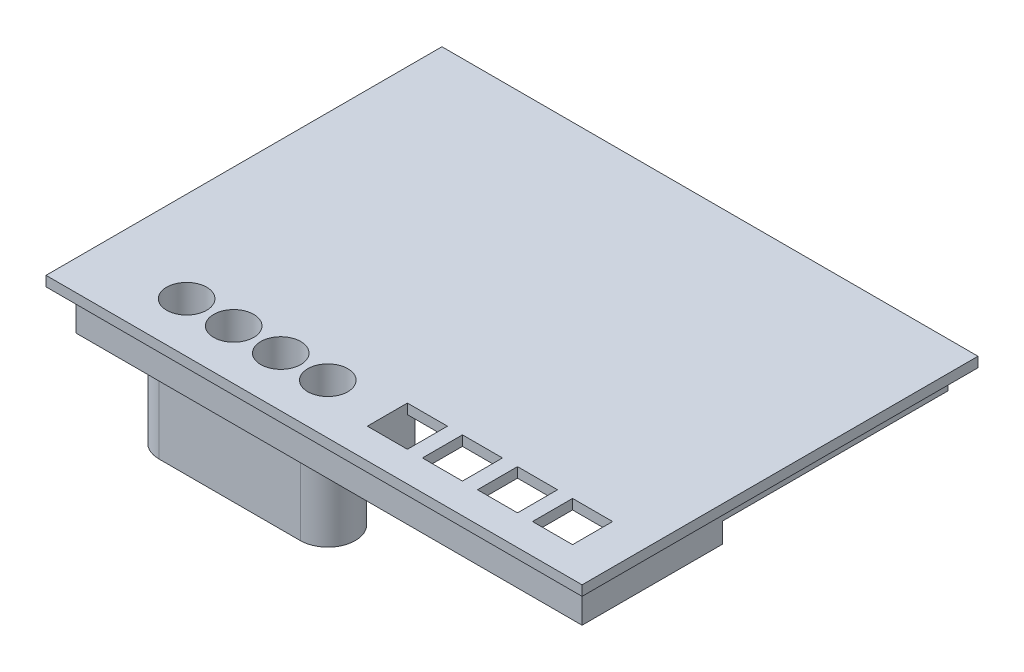
SolidWorks part; units mm, degrees
ref_plane "Front Plane" through (0, 0, 0) normal (0, 0, 1) x (1, 0, 0)
ref_plane "Top Plane" through (0, 0, 0) normal (0, 1, 0) x (1, 0, 0)
ref_plane "Right Plane" through (0, 0, 0) normal (1, 0, 0) x (0, 0, -1)
sketch "Sketch1" plane through (0, 0, 0) normal (0, 1, 0) x (1, 0, 0)
  line L1 (-39.05, -27.95) -> (39.05, -27.95)
  line L2 (-39.05, -27.95) -> (-39.05, 27.95)
  line L3 (-39.05, 27.95) -> (39.05, 27.95)
  line L4 (39.05, -27.95) -> (39.05, 27.95)
  line L5 (-39.05, -27.95) -> (39.05, 27.95) construction
  line L6 (-39.05, 27.95) -> (39.05, -27.95) construction
  point P0 (0, 0)
extrude "Boss-Extrude1" add sketch "Sketch1" along normal blind 3
sketch "Sketch2" plane through (0, 3, 0) normal (0, 1, 0) x (1, 0, 0)
  circle A0 centre (-35.9, 20.9) radius 1.25
  circle A1 centre (-35.9, -24.8) radius 1.25
  circle A2 centre (35.9, -24.8) radius 1.25
  circle A3 centre (35.9, 24.8) radius 1.25
extrude "Cut-Extrude1" cut sketch "Sketch2" against normal blind 68
sketch "Sketch3" plane through (0, 3, 0) normal (0, 1, 0) x (1, 0, 0)
  line L0 (-39.05, -27.95) -> (39.05, -27.95) construction
  line L5 (-31.15, -27.95) -> (8.45, -27.95)
  line L6 (-31.15, -27.95) -> (-31.15, -12.75)
  line L7 (-31.15, -12.75) -> (8.45, -12.75)
  line L8 (8.45, -27.95) -> (8.45, -12.75)
  line L13 (27.35, -17.65) -> (15.85, -17.65)
  line L14 (27.35, -17.65) -> (27.35, -27.95)
  line L15 (27.35, -27.95) -> (15.85, -27.95)
  line L16 (15.85, -17.65) -> (15.85, -27.95)
  line L18 (-39.05, 27.95) -> (39.05, 27.95)
  line L19 (-39.05, 27.95) -> (-39.05, -27.95)
  line L20 (-39.05, -27.95) -> (39.05, -27.95)
  line L21 (39.05, 27.95) -> (39.05, -27.95)
  line L22 (-31.15, -27.95) -> (-25.45, -27.95)
  line L23 (-31.15, -27.95) -> (-31.15, -20.45)
  line L24 (-31.15, -20.45) -> (-25.45, -20.45)
  line L25 (-25.45, -27.95) -> (-25.45, -20.45)
  line L26 (8.45, -27.95) -> (2.75, -27.95)
  line L27 (8.45, -27.95) -> (8.45, -20.45)
  line L28 (8.45, -20.45) -> (2.75, -20.45)
  line L29 (2.75, -27.95) -> (2.75, -20.45)
  line L30 (2.75, -27.95) -> (-6.65, -27.95)
  line L31 (2.75, -27.95) -> (2.75, -20.45)
  line L32 (2.75, -20.45) -> (-6.65, -20.45)
  line L33 (-6.65, -27.95) -> (-6.65, -20.45)
  line L34 (-25.45, -27.95) -> (-16.05, -27.95)
  line L35 (-25.45, -27.95) -> (-25.45, -20.45)
  line L36 (-25.45, -20.45) -> (-16.05, -20.45)
  line L37 (-16.05, -27.95) -> (-16.05, -20.45)
  circle A0 centre (35.9, 24.8) radius 1.25
  circle A1 centre (35.9, -24.8) radius 1.25
  circle A2 centre (-35.9, -24.8) radius 1.25
  circle A3 centre (-35.9, 20.9) radius 1.25
  circle A4 centre (2.75, -20.45) radius 4
  circle A5 centre (-6.65, -20.45) radius 4
  circle A6 centre (-16.05, -20.45) radius 4
  circle A7 centre (-25.45, -20.45) radius 4
sketch "Sketch4" plane through (0, 0, 0) normal (0, -1, 0) x (-1, 0, 0)
  line L0 (0, -27.95) -> (0, -29.95) construction
  line L1 (39.05, 27.95) -> (-39.05, 27.95)
  line L2 (39.05, 27.95) -> (39.05, -27.95)
  line L3 (39.05, -27.95) -> (-39.05, -27.95)
  line L4 (-39.05, 27.95) -> (-39.05, -27.95)
  line L5 (39.05, 27.95) -> (-39.05, -27.95) construction
  line L6 (39.05, -27.95) -> (-39.05, 27.95) construction
  line L7 (41.05, 29.95) -> (-41.05, 29.95)
  line L8 (41.05, 29.95) -> (41.05, -29.95)
  line L9 (41.05, -29.95) -> (-41.05, -29.95)
  line L10 (-41.05, 29.95) -> (-41.05, -29.95)
  line L11 (41.05, 29.95) -> (-41.05, -29.95) construction
  line L12 (41.05, -29.95) -> (-41.05, 29.95) construction
  line L13 (-39.05, 0) -> (-41.05, 0) construction
  point P0 (0, 0)
  point P7 (0, 0)
extrude "Boss-Extrude3" add sketch "Sketch4" against normal blind 3
sketch "Sketch6" plane through (0, 3, 0) normal (0, 1, 0) x (1, 0, 0)
  circle A0 centre (-35.9, -24.8) radius 1.25
  circle A1 centre (35.9, -24.8) radius 1.25
  circle A2 centre (35.9, 24.8) radius 1.25
  circle A3 centre (-35.9, 20.9) radius 1.25
  circle A4 centre (-35.9, 20.9) radius 3
  circle A5 centre (35.9, 24.8) radius 3
  circle A6 centre (35.9, -24.8) radius 3
  circle A7 centre (-35.9, -24.8) radius 3
extrude "Boss-Extrude4" add sketch "Sketch6" along normal blind 3.5
sketch "Sketch7" plane through (0, 0, 0) normal (0, -1, 0) x (-1, 0, 0)
  line L1 (-41.05, 29.95) -> (41.05, 29.95)
  line L2 (-41.05, 29.95) -> (-41.05, 46.15)
  line L3 (-41.05, 46.15) -> (41.05, 46.15)
  line L4 (41.05, 29.95) -> (41.05, 46.15)
extrude "Boss-Extrude5" add sketch "Sketch7" against normal blind 3
sketch "Sketch8" plane through (0, 0, -46.15) normal (0, 0, -1) x (-1, 0, 0)
  line L1 (-41.05, 0) -> (41.05, 0)
  line L2 (-41.05, 0) -> (-41.05, 50.5)
  line L3 (-41.05, 50.5) -> (41.05, 50.5)
  line L4 (41.05, 0) -> (41.05, 50.5)
extrude "Boss-Extrude6" add sketch "Sketch8" along normal blind 3
sketch "Sketch10" plane through (41.05, 0, 0) normal (1, 0, 0) x (0, 0, -1)
  line L1 (46.15, 50.5) -> (49.15, 50.5)
  line L2 (46.15, 50.5) -> (46.15, 0)
  line L3 (46.15, 0) -> (49.15, 0)
  line L4 (49.15, 50.5) -> (49.15, 0)
  line L5 (-29.95, 0) -> (46.15, 0)
  line L6 (-29.95, 0) -> (-29.95, 3)
  line L7 (-29.95, 3) -> (46.15, 3)
  line L8 (46.15, 0) -> (46.15, 3)
  line M1 (-29.95, 0) -> (49.15, 0)
  line M5 (46.15, 3) -> (-29.95, 3)
  line M6 (-29.95, 3) -> (-29.95, 0)
extrude "Boss-Extrude7" add sketch "Sketch10" along normal blind 20 contours L2 M5 M6 M1
sketch "Sketch12" plane through (-41.05, 0, 0) normal (-1, 0, 0) x (0, 0, 1)
  line L1 (-49.15, 50.5) -> (29.95, 50.5)
  line L2 (-49.15, 50.5) -> (-49.15, 0)
  line L3 (-49.15, 0) -> (29.95, 0)
  line L4 (29.95, 50.5) -> (29.95, 0)
extrude "Boss-Extrude8" add sketch "Sketch12" along normal blind 3
sketch "Sketch17" plane through (0, 0, 29.95) normal (0, 0, 1) x (1, 0, 0)
  line L1 (-44.05, 50.5) -> (61.05, 50.5)
  line L2 (-44.05, 50.5) -> (-44.05, 0)
  line L3 (-44.05, 0) -> (61.05, 0)
  line L4 (61.05, 50.5) -> (61.05, 0)
extrude "Boss-Extrude13" add sketch "Sketch17" against normal blind 2 and the other way blind 1
sketch "Sketch18" plane through (0, 0, 27.95) normal (0, 0, -1) x (-1, 0, 0)
  line L0 (-61.05, 3) -> (-61.05, 50.5) construction
  line L1 (41.05, 3) -> (-61.05, 3)
  line L2 (41.05, 3) -> (41.05, 6.5)
  line L4 (-61.05, 3) -> (-61.05, 6.5)
  line L10 (-8.45, 8.1) -> (-8.45, 13.1) construction
  line L19 (-8.45, 8.1) -> (-8.45, 22.1) construction
  line L21 (-8.45, 22.1) -> (31.15, 22.1)
  line L22 (-8.45, 22.1) -> (-8.45, 13.1)
  line L23 (-8.45, 13.1) -> (31.15, 13.1)
  line L24 (31.15, 22.1) -> (31.15, 13.1)
  line L31 (-25.35, 8.1) -> (-17.85, 11.8) construction
  line L32 (-25.35, 11.8) -> (-17.85, 8.1) construction
  line L38 (-27.35, 6.1) -> (-15.85, 6.1)
  line L39 (-27.35, 6.1) -> (-27.35, 13.8)
  line L40 (-27.35, 13.8) -> (-15.85, 13.8)
  line L41 (-15.85, 6.1) -> (-15.85, 13.8)
  line L42 (-27.35, 6.1) -> (-15.85, 13.8) construction
  line L43 (-27.35, 13.8) -> (-15.85, 6.1) construction
  point P7 (-21.6, 9.95)
  point P8 (-21.6, 9.95)
  point P27 (-21.6, 9.95)
  point P32 (-21.6, 9.95)
extrude "Cut-Extrude4" cut sketch "Sketch18" against normal blind 9 contours L38 L41 L40 L39 | L24 L21 L22 L23
sketch "Sketch19" plane through (61.05, 0, 0) normal (1, 0, 0) x (0, 0, -1)
  line L1 (-30.95, 50.5) -> (49.15, 50.5)
  line L2 (-30.95, 50.5) -> (-30.95, 0)
  line L3 (-30.95, 0) -> (49.15, 0)
  line L4 (49.15, 50.5) -> (49.15, 0)
extrude "Boss-Extrude14" add sketch "Sketch19" along normal blind 3
sketch "Sketch20" plane through (61.05, 0, 0) normal (-1, 0, 0) x (0, 0, 1)
  line L0 (-34.985, 3) -> (-34.985, 5) construction
  line L1 (-46.15, 3) -> (27.95, 3) construction
  line L2 (-46.15, 21.4946) -> (-44.15, 21.4946) construction
  line L3 (-46.15, 50.5) -> (-46.15, 3) construction
  line L4 (-44.15, 45) -> (-4.15, 5) construction
  line L14 (-39.9, 9.25) -> (-8.4, 40.75) construction
  line L15 (-39.9, 40.75) -> (-8.4, 9.25) construction
  circle A0 centre (-24.15, 25) radius 19
  circle A1 centre (-8.4, 40.75) radius 1.5
  circle A2 centre (-39.9, 40.75) radius 1.5
  circle A3 centre (-8.4, 9.25) radius 1.5
  circle A4 centre (-39.9, 9.25) radius 1.5
extrude "Cut-Extrude5" cut sketch "Sketch20" against normal blind 3
sketch "Sketch22" plane through (-41.05, 0, 0) normal (1, 0, 0) x (0, 0, -1)
  line L0 (46.15, 3) -> (27.95, 3) construction
  line L1 (-27.95, 3) -> (46.15, 3) construction
  line L2 (27.95, 3) -> (9.95, 3) construction
  line L3 (46.15, 26.75) -> (44.15, 26.75) construction
  line L4 (46.15, 3) -> (46.15, 50.5) construction
  line L5 (9.95, 45.5) -> (9.95, 36.125) construction
  line L6 (-27.95, 50.5) -> (46.15, 50.5) construction
  line L7 (44.15, 3) -> (44.15, 50.5) construction
  line L8 (18.5, 50.5) -> (18.5, 3) construction
  line L9 (9.95, 50.5) -> (18.5, 50.5) construction
  line L10 (27.05, 50.5) -> (27.05, 3) construction
  line L11 (18.5, 50.5) -> (27.05, 50.5) construction
  line L12 (35.6, 50.5) -> (35.6, 3) construction
  line L13 (27.05, 50.5) -> (35.6, 50.5) construction
  line L14 (35.6, 50.5) -> (44.15, 50.5) construction
  line L15 (14.225, 50.5) -> (14.225, 3) construction
  line L16 (22.775, 50.5) -> (22.775, 3) construction
  line L17 (31.325, 50.5) -> (31.325, 3) construction
  line L18 (39.875, 50.5) -> (39.875, 3) construction
  line L19 (9.95, 26.75) -> (44.15, 26.75) construction
  line L20 (9.95, 36.125) -> (9.95, 26.75) construction
  line L21 (9.95, 45.5) -> (44.15, 45.5) construction
  line L22 (9.95, 8) -> (44.15, 8) construction
  line L23 (9.95, 17.375) -> (44.15, 17.375) construction
  line L24 (9.95, 36.125) -> (44.15, 36.125) construction
  line L25 (9.95, 26.75) -> (9.95, 17.375) construction
  line L26 (9.95, 17.375) -> (9.95, 8) construction
  line L27 (9.95, 40.8125) -> (44.15, 40.8125) construction
  line L28 (9.95, 31.4375) -> (44.15, 31.4375) construction
  line L29 (9.95, 22.0625) -> (44.15, 22.0625) construction
  line L30 (9.95, 12.6875) -> (44.15, 12.6875) construction
  circle A0 centre (14.225, 12.6875) radius 2.5
  circle A1 centre (14.225, 22.0625) radius 2.5
  circle A2 centre (18.5, 17.375) radius 2.5
  circle A3 centre (22.775, 22.0625) radius 2.5
  circle A4 centre (22.775, 12.6875) radius 2.5
  circle A5 centre (14.225, 31.4375) radius 2.5
  circle A6 centre (18.5, 26.75) radius 2.5
  circle A7 centre (22.775, 31.4375) radius 2.5
  circle A8 centre (18.5, 36.125) radius 2.5
  circle A9 centre (14.225, 40.8125) radius 2.5
  circle A10 centre (22.775, 40.8125) radius 2.5
  circle A11 centre (27.05, 36.125) radius 2.5
  circle A12 centre (31.325, 40.8125) radius 2.5
  circle A13 centre (39.875, 40.8125) radius 2.5
  circle A14 centre (35.6, 36.125) radius 2.5
  circle A15 centre (39.875, 31.4375) radius 2.5
  circle A16 centre (31.325, 31.4375) radius 2.5
  circle A17 centre (27.05, 26.75) radius 2.5
  circle A18 centre (31.325, 22.0625) radius 2.5
  circle A19 centre (39.875, 22.0625) radius 2.5
  circle A20 centre (35.6, 26.75) radius 2.5
  circle A21 centre (27.05, 17.375) radius 2.5
  circle A22 centre (31.325, 12.6875) radius 2.5
  circle A23 centre (39.875, 12.6875) radius 2.5
  circle A24 centre (35.6, 17.375) radius 2.5
  circle A26 centre (18.5, 8) radius 2.5
  circle A27 centre (27.05, 8) radius 2.5
  circle A28 centre (35.6, 8) radius 2.5
extrude "Cut-Extrude6" cut sketch "Sketch22" against normal blind 3
sketch "Sketch23" plane through (64.05, 0, 0) normal (1, 0, 0) x (0, 0, -1)
  circle A0 centre (8.4, 9.25) radius 1.5
  circle A1 centre (39.9, 40.75) radius 1.5
extrude "Boss-Extrude16" add sketch "Sketch23" against normal blind 3
sketch "Sketch25" plane through (0, 0, 30.95) normal (0, 0, 1) x (1, 0, 0)
  line L1 (-44.05, 50.5) -> (64.05, 50.5)
  line L2 (-44.05, 50.5) -> (-44.05, 0)
  line L3 (-44.05, 0) -> (64.05, 0)
  line L4 (64.05, 50.5) -> (64.05, 0)
extrude "Cut-Extrude8" cut sketch "Sketch25" against normal blind 0.5
sketch "Sketch26" plane through (64.05, 0, 0) normal (1, 0, 0) x (0, 0, -1)
  line L1 (-30.45, 50.5) -> (49.15, 50.5)
  line L2 (-30.45, 50.5) -> (-30.45, 0)
  line L3 (-30.45, 0) -> (49.15, 0)
  line L4 (49.15, 50.5) -> (49.15, 0)
extrude "Cut-Extrude9" cut sketch "Sketch26" against normal blind 0.5
sketch "Sketch27" plane through (0, 0, -49.15) normal (0, 0, -1) x (-1, 0, 0)
  line L1 (-63.55, 50.5) -> (44.05, 50.5)
  line L2 (-63.55, 50.5) -> (-63.55, 0)
  line L3 (-63.55, 0) -> (44.05, 0)
  line L4 (44.05, 50.5) -> (44.05, 0)
extrude "Cut-Extrude10" cut sketch "Sketch27" against normal blind 0.5
sketch "Sketch28" plane through (-44.05, 0, 0) normal (-1, 0, 0) x (0, 0, 1)
  line L1 (-48.65, 50.5) -> (30.45, 50.5)
  line L2 (-48.65, 50.5) -> (-48.65, 0)
  line L3 (-48.65, 0) -> (30.45, 0)
  line L4 (30.45, 50.5) -> (30.45, 0)
extrude "Cut-Extrude11" cut sketch "Sketch28" against normal blind 0.5
sketch "Sketch30" plane through (0, 50.5, 0) normal (0, 1, 0) x (1, 0, 0)
  line L0 (61.05, 46.15) -> (-41.05, -27.95) construction
  line L1 (10, -27.45) -> (10, -27.95) construction
  line L2 (-40.55, 45.65) -> (60.55, 45.65)
  line L3 (-40.55, 45.65) -> (-40.55, -27.45)
  line L4 (-40.55, -27.45) -> (60.55, -27.45)
  line L5 (60.55, 45.65) -> (60.55, -27.45)
  line L6 (-40.55, 45.65) -> (60.55, -27.45) construction
  line L7 (-40.55, -27.45) -> (60.55, 45.65) construction
  line L8 (61.05, -27.95) -> (-41.05, -27.95) construction
  line L9 (60.55, 9.1) -> (61.05, 9.1) construction
  line L10 (61.05, 46.15) -> (61.05, -27.95) construction
  point P4 (10, 9.1)
extrude "Boss-Extrude17" add sketch "Sketch30" along normal blind 2 and the other way blind 6 separate body
sketch "Sketch31" plane through (0, 3, 0) normal (0, 1, 0) x (1, 0, 0)
  line L1 (-31.15, -12.75) -> (8.45, -12.75)
  line L2 (-31.15, -12.75) -> (-31.15, -27.95)
  line L3 (-31.15, -27.95) -> (8.45, -27.95)
  line L4 (8.45, -12.75) -> (8.45, -27.95)
extrude "Cut-Extrude12" cut sketch "Sketch31" against normal blind 18
sketch "Sketch32" plane through (0, 0, 0) normal (0, -1, 0) x (1, 0, 0)
  circle A0 centre (2.73, 16.5811) radius 4
  circle A1 centre (-6.6072, 16.5811) radius 4
  circle A2 centre (-16.03, 16.55) radius 4
  circle A3 centre (-25.43, 16.55) radius 4
extrude "Cut-Extrude13" cut sketch "Sketch32" against normal blind 788
sketch "Sketch35" plane through (0, 0, 30.45) normal (0, 0, 1) x (1, 0, 0)
  line L0 (10, 50.5) -> (10, 44.5) construction
  line L1 (63.55, 50.5) -> (-43.55, 50.5) construction
  line L2 (-43.55, 0) -> (-43.55, 50.5) construction
  line L3 (-43.55, 44.5) -> (84.6873, 44.5)
  line L4 (-43.55, 44.5) -> (-43.55, -56.9173)
  line L5 (-43.55, -56.9173) -> (84.6873, -56.9173)
  line L6 (84.6873, 44.5) -> (84.6873, -56.9173)
extrude "Cut-Extrude16" cut sketch "Sketch35" against normal blind 109
sketch "Sketch36" plane through (0, 50.5, 0) normal (0, 1, 0) x (1, 0, 0)
  line L1 (-43.55, 48.65) -> (63.55, 48.65)
  line L2 (-43.55, 48.65) -> (-43.55, -30.45)
  line L3 (-43.55, -30.45) -> (63.55, -30.45)
  line L4 (63.55, 48.65) -> (63.55, -30.45)
  line L5 (61.05, -27.95) -> (-41.05, -27.95)
  line L6 (61.05, -27.95) -> (61.05, 46.15)
  line L7 (61.05, 46.15) -> (-41.05, 46.15)
  line L8 (-41.05, -27.95) -> (-41.05, 46.15)
extrude "Boss-Extrude18" add sketch "Sketch36" along normal blind 2
sketch "Sketch37" plane through (0, 44.5, 0) normal (0, -1, 0) x (-1, 0, 0)
  line L1 (43.55, -30.45) -> (-63.55, -30.45)
  line L2 (43.55, -30.45) -> (43.55, 48.65)
  line L3 (43.55, 48.65) -> (-63.55, 48.65)
  line L4 (-63.55, -30.45) -> (-63.55, 48.65)
  line L5 (-61.05, 46.15) -> (41.05, 46.15)
  line L6 (-61.05, 46.15) -> (-61.05, -27.95)
  line L7 (-61.05, -27.95) -> (41.05, -27.95)
  line L8 (41.05, 46.15) -> (41.05, -27.95)
extrude "Cut-Extrude17" cut sketch "Sketch37" against normal blind 6
sketch "Sketch38" plane through (0, 52.5, 0) normal (0, 1, 0) x (1, 0, 0)
  line L1 (61.05, -27.95) -> (-41.05, -27.95)
  line L2 (61.05, -27.95) -> (61.05, 46.15)
  line L3 (61.05, 46.15) -> (-41.05, 46.15)
  line L4 (-41.05, -27.95) -> (-41.05, 46.15)
  line L5 (-32.3027, -6.1655) -> (10, -6.1655)
  line L6 (-32.3027, -6.1655) -> (-32.3027, -24.9297)
  line L7 (-32.3027, -24.9297) -> (10, -24.9297)
  line L8 (10, -6.1655) -> (10, -24.9297)
extrude "Boss-Extrude19" add sketch "Sketch38" against normal blind 2
sketch "Sketch39" plane through (0, 44.5, 0) normal (0, -1, 0) x (-1, 0, 0)
  line L0 (40.55, -27.45) -> (-60.55, 45.65) construction
  line L5 (-10, 45.65) -> (-10, 44.15) construction
  line L6 (-60.55, 9.1) -> (-59.05, 9.1) construction
  line L7 (-10, -27.45) -> (-10, -25.95) construction
  line L9 (39.05, 44.15) -> (-59.05, 44.15)
  line L10 (39.05, 44.15) -> (39.05, -25.95)
  line L11 (39.05, -25.95) -> (-59.05, -25.95)
  line L12 (-59.05, 44.15) -> (-59.05, -25.95)
  line L13 (39.05, 44.15) -> (-59.05, -25.95) construction
  line L14 (39.05, -25.95) -> (-59.05, 44.15) construction
  point P12 (-10, 9.1)
extrude "Cut-Extrude18" cut sketch "Sketch39" against normal blind 6
sketch "Sketch40" plane through (0, 50.5, 0) normal (0, -1, 0) x (-1, 0, 0)
  line L0 (25.43, -11.1817) -> (-2.73, -11.2439)
  line L1 (-2.73, -21.9183) -> (25.43, -21.9183)
  circle A0 centre (-2.73, -16.5811) radius 4
  circle A1 centre (6.6072, -16.5811) radius 4
  circle A3 centre (25.43, -16.55) radius 4
  circle A4 centre (-2.73, -16.5811) radius 5.3372
  circle A5 centre (25.43, -16.55) radius 5.3683
  circle A6 centre (16.03, -16.55) radius 4
  circle M4 centre (16.03, -16.55) radius 4
  circle M5 centre (-2.73, -16.5811) radius 4
  circle M10 centre (6.6072, -16.5811) radius 4
  circle M11 centre (25.43, -16.55) radius 4
extrude "Boss-Extrude21" add sketch "Sketch40" along normal blind 20 contours A5 L0 A4 L1 M10 M4 | A4 M5 | L0 A5 M11
sketch "Sketch43" plane through (59.05, 0, 0) normal (-1, 0, 0) x (0, 0, 1)
  line L5 (-0.65, 46) -> (-44.15, 46)
  line L6 (-0.65, 46) -> (-0.65, 44.5)
  line L7 (-0.65, 44.5) -> (-44.15, 44.5)
  line L8 (-44.15, 46) -> (-44.15, 44.5)
extrude "Cut-Extrude19" cut sketch "Sketch43" against normal blind 20
sketch "Sketch44" plane through (0, 0, -44.15) normal (0, 0, 1) x (1, 0, 0)
  line L0 (-39.05, 44.5) -> (60.55, 44.5) construction
  line L1 (60.55, 46) -> (38.55, 46)
  line L2 (60.55, 46) -> (60.55, 44.5)
  line L3 (60.55, 44.5) -> (38.55, 44.5)
  line L4 (38.55, 46) -> (38.55, 44.5)
extrude "Cut-Extrude20" cut sketch "Sketch44" against normal blind 20
fillet "Fillet1" radius 3 4 edges at (-30.7983, 50.5, 16.55) (-11.35, 50.5, 21.9183) (8.0672, 50.5, 16.5811) (-11.35, 50.5, 11.2128)
sketch "Sketch45" plane through (0, 50.5, 0) normal (0, -1, 0) x (-1, 0, 0)
  line L1 (39.05, -25.95) -> (-34.2088, -25.95)
  line L2 (39.05, -25.95) -> (39.05, 18.7182)
  line L3 (39.05, 18.7182) -> (-34.2088, 18.7182)
  line L4 (-34.2088, -25.95) -> (-34.2088, 18.7182)
extrude "Cut-Extrude21" cut sketch "Sketch45" along normal blind 63
extrude "Cut-Extrude22" cut sketch "Sketch3" against normal blind 374 and the other way blind 380 contours L36 A7 L24 | L24 A7 L35 | L35 A7 L36 | L36 A6 L37 | L37 A6 L36 | L32 A5 L33 | L33 A5 L32 | L32 A4 L31 | L31 A4 L28 | L28 A4 L32
sketch "Sketch49" plane through (0, 50.5, 0) normal (0, -1, 0) x (-1, 0, 0)
  circle A0 centre (25.45, -20.45) radius 4
  circle A1 centre (16.05, -20.45) radius 4
  circle A2 centre (6.65, -20.45) radius 4
  circle A3 centre (-2.75, -20.45) radius 4
  circle A4 centre (-2.73, -16.5811) radius 4
  circle A5 centre (6.6072, -16.5811) radius 4
  circle A6 centre (16.03, -16.55) radius 4
  circle A7 centre (25.43, -16.55) radius 4
  arc M3 (21.9476, -18.5179) -> (28.9324, -18.4821) centre (25.43, -16.55) cw
  arc M5 (12.5476, -18.5179) -> (19.5324, -18.4821) centre (16.03, -16.55) cw
  arc M7 (3.1277, -18.5543) -> (10.1294, -18.4768) centre (6.6072, -16.5811) cw
  arc M9 (-6.2411, -18.4974) -> (0.7611, -18.5336) centre (-2.73, -16.5811) cw
extrude "Boss-Extrude23" add sketch "Sketch49" against normal blind 2 contours A3 M9 | A2 M7 | A1 M5 | A0 M3
sketch "Sketch50" plane through (0, 50.5, 0) normal (0, -1, 0) x (-1, 0, 0)
  line L0 (25.45, -14.95) -> (-2.75, -14.95)
  line L1 (-2.75, -25.95) -> (25.45, -25.95)
  circle A0 centre (-2.75, -20.45) radius 5.5
  circle A1 centre (25.45, -20.45) radius 5.5
  circle M1 centre (25.45, -20.45) radius 4
  circle M2 centre (16.05, -20.45) radius 4
  circle M3 centre (6.65, -20.45) radius 4
  circle M4 centre (-2.75, -20.45) radius 4
  line M8 (-59.05, -25.95) -> (39.05, -25.95)
extrude "Boss-Extrude24" add sketch "Sketch50" along normal blind 23 contours A1 L0 A0 M3 M8 M2 | A1 M2 M1 | A0 M3 M4
fillet "Fillet2" radius 3 3 edges at (-30.95, 50.5, 20.45) (-11.35, 50.5, 14.95) (8.25, 50.5, 20.45)
sketch "Sketch51" plane through (0, 0, -45.65) normal (0, 0, -1) x (-1, 0, 0)
  line L0 (-60.55, 46) -> (-60.55, 50.5) construction
  line L1 (-38.55, 46) -> (-60.55, 46)
  line L2 (-38.55, 46) -> (-38.55, 46.5)
  line L3 (-38.55, 46.5) -> (-60.55, 46.5)
  line L4 (-60.55, 46) -> (-60.55, 46.5)
extrude "Cut-Extrude23" cut sketch "Sketch51" against normal blind 23
sketch "Sketch52" plane through (60.55, 0, 0) normal (1, 0, 0) x (0, 0, -1)
  line L1 (22.65, 46.5) -> (0.65, 46.5)
  line L2 (22.65, 46.5) -> (22.65, 46)
  line L3 (22.65, 46) -> (0.65, 46)
  line L4 (0.65, 46.5) -> (0.65, 46)
extrude "Cut-Extrude24" cut sketch "Sketch52" against normal blind 23
sketch "Sketch53" plane through (0, 52.5, 0) normal (0, 1, 0) x (1, 0, 0)
  line L0 (63.55, -24.45) -> (6.75, -24.45) construction
  line L1 (63.55, -30.45) -> (63.55, 48.65) construction
  line L2 (6.75, -24.45) -> (6.75, -20.45) construction
  line L3 (6.75, -20.45) -> (6.75, -16.45) construction
  line L4 (6.75, -16.45) -> (63.55, -16.45) construction
  line L5 (33.65, -20.45) -> (36.65, -20.45)
  line L6 (35.15, -24.45) -> (35.15, -16.45) construction
  line L7 (36.65, -20.45) -> (44.65, -20.45) construction
  line L8 (44.65, -20.45) -> (47.65, -20.45) construction
  line L9 (47.65, -20.45) -> (55.65, -20.45) construction
  line L10 (33.65, -20.45) -> (25.65, -20.45) construction
  line L11 (25.65, -20.45) -> (22.65, -20.45) construction
  line L12 (22.65, -20.45) -> (14.65, -20.45) construction
  line L14 (22.65, -24.45) -> (14.65, -24.45)
  line L15 (22.65, -24.45) -> (22.65, -16.45)
  line L16 (22.65, -16.45) -> (14.65, -16.45)
  line L17 (14.65, -24.45) -> (14.65, -16.45)
  line L18 (22.65, -24.45) -> (14.65, -16.45) construction
  line L19 (22.65, -16.45) -> (14.65, -24.45) construction
  line L20 (33.65, -24.45) -> (25.65, -24.45)
  line L21 (33.65, -24.45) -> (33.65, -16.45)
  line L22 (33.65, -16.45) -> (25.65, -16.45)
  line L23 (25.65, -24.45) -> (25.65, -16.45)
  line L24 (33.65, -24.45) -> (25.65, -16.45) construction
  line L25 (33.65, -16.45) -> (25.65, -24.45) construction
  line L26 (44.65, -24.45) -> (36.65, -24.45)
  line L27 (44.65, -24.45) -> (44.65, -16.45)
  line L28 (44.65, -16.45) -> (36.65, -16.45)
  line L29 (36.65, -24.45) -> (36.65, -16.45)
  line L30 (44.65, -24.45) -> (36.65, -16.45) construction
  line L31 (44.65, -16.45) -> (36.65, -24.45) construction
  line L32 (55.65, -24.45) -> (47.65, -24.45)
  line L33 (55.65, -24.45) -> (55.65, -16.45)
  line L34 (55.65, -16.45) -> (47.65, -16.45)
  line L35 (47.65, -24.45) -> (47.65, -16.45)
  line L36 (55.65, -24.45) -> (47.65, -16.45) construction
  line L37 (55.65, -16.45) -> (47.65, -24.45) construction
  circle A0 centre (2.75, -20.45) radius 4 construction
  point P10 (18.65, -20.45)
  point P14 (35.15, -20.45)
  point P25 (29.65, -20.45)
  point P30 (40.65, -20.45)
  point P35 (51.65, -20.45)
extrude "Cut-Extrude25" cut sketch "Sketch53" against normal blind 23 contours L35 L32 L33 L34 | L29 L26 L27 L28 | L23 L20 L21 L22 | L17 L14 L15 L16
sketch "Sketch54" plane through (0, 27.5, 0) normal (0, -1, 0) x (-1, 0, 0)
  line L0 (-2.75, -14.95) -> (25.45, -14.95)
  line L2 (35.5013, -14.95) -> (-14.2013, -14.95)
  line L3 (35.5013, -14.95) -> (35.5013, -25.95)
  line L4 (35.5013, -25.95) -> (-14.2013, -25.95)
  line L5 (-14.2013, -14.95) -> (-14.2013, -25.95)
  line L6 (35.5013, -14.95) -> (-14.2013, -25.95) construction
  line L7 (35.5013, -25.95) -> (-14.2013, -14.95) construction
  line L8 (35.5013, -14.95) -> (-14.2013, -14.95)
  line L9 (35.5013, -14.95) -> (35.5013, -4.0672)
  line L10 (35.5013, -4.0672) -> (-14.2013, -4.0672)
  line L11 (-14.2013, -14.95) -> (-14.2013, -4.0672)
  circle A0 centre (25.45, -20.45) radius 5.5
  circle A1 centre (-2.75, -20.45) radius 5.5
  circle A2 centre (6.65, -20.45) radius 4 construction
  point P10 (10.65, -20.45)
  line M3 (25.45, -14.95) -> (-2.75, -14.95)
  arc M4 (-2.75, -14.95) -> (-2.75, -25.95) centre (-2.75, -20.45) ccw
  arc M6 (25.45, -25.95) -> (25.45, -14.95) centre (25.45, -20.45) ccw
extrude "Cut-Extrude26" cut sketch "Sketch54" against normal blind 23 contours L11 L2 L9 L10 M3 | L4 L3 L2 M6 | L2 L5 L4 M4
sketch "Sketch56" plane through (0, 50.5, 0) normal (0, -1, 0) x (1, 0, 0)
  line L0 (59.05, -44.15) -> (59.05, 25.95) construction
  line L1 (55.65, 24.45) -> (59.05, 24.45)
  line L2 (55.65, 24.45) -> (55.65, 25.95)
  line L3 (55.65, 25.95) -> (59.05, 25.95)
  line L4 (59.05, 24.45) -> (59.05, 25.95)
  line L5 (55.65, 24.45) -> (59.05, 24.45)
  line L6 (55.65, 24.45) -> (55.65, 16.45)
  line L7 (55.65, 16.45) -> (59.05, 16.45)
  line L8 (59.05, 24.45) -> (59.05, 16.45)
  line L10 (59.05, 16.45) -> (55.65, 16.45)
  line L11 (59.05, 16.45) -> (59.05, 14.95)
  line L12 (59.05, 14.95) -> (55.65, 14.95)
  line L13 (55.65, 16.45) -> (55.65, 14.95)
  line M9 (59.05, 25.95) -> (2.75, 25.95)
  line M16 (59.05, -44.15) -> (59.05, 25.95)
  line M19 (55.65, 24.45) -> (55.65, 16.45)
extrude "Boss-Extrude25" add sketch "Sketch56" along normal blind 6 contours L2 L1 M16 M9 | L7 L1 M19 M16 | L7 L13 L12 M16
sketch "Sketch58" plane through (0, 50.5, 0) normal (0, -1, 0) x (1, 0, 0)
  line L0 (55.65, 25.95) -> (2.75, 25.95) construction
  line L1 (14.65, 25.95) -> (9.75, 25.95)
  line L2 (14.65, 25.95) -> (14.65, 14.95)
  line L3 (14.65, 14.95) -> (9.75, 14.95)
  line L4 (9.75, 25.95) -> (9.75, 14.95)
sketch "Sketch59" plane through (0, 44.5, 0) normal (0, -1, 0) x (-1, 0, 0)
extrude "Boss-Extrude26" add sketch "Sketch58" along normal blind 6
sketch "Sketch61" plane through (0, 44.5, 0) normal (0, -1, 0) x (-1, 0, 0)
  line L0 (-14.65, -25.95) -> (-9.75, -25.95) construction
  line L1 (-55.65, -25.95) -> (-60.55, -25.95) construction
  line L2 (-60.55, -27.45) -> (-60.55, 0.65) construction
  line L3 (-58.1, -25.95) -> (-58.1, -14.95) construction
  line L4 (-59.05, -14.95) -> (-55.65, -14.95) construction
  line L5 (-12.2, -25.95) -> (-12.2, -14.95) construction
  line L6 (-9.75, -14.95) -> (-14.65, -14.95) construction
  line L7 (-12.2, -20.45) -> (-58.1, -20.45) construction
  line L8 (-58.15, -20.45) -> (-12.15, -20.45)
  circle A0 centre (-58.15, -20.45) radius 1
  circle A1 centre (-12.15, -20.45) radius 1
  point P22 (-35.15, -20.45)
extrude "Cut-Extrude27" cut sketch "Sketch61" against normal blind 6
sketch "Sketch62" plane through (0, 44.5, 0) normal (0, -1, 0) x (-1, 0, 0)
  line L1 (-55.65, -14.95) -> (-59.05, -14.95)
  line L2 (-55.65, -14.95) -> (-55.65, 0.65)
  line L3 (-55.65, 0.65) -> (-59.05, 0.65)
  line L4 (-59.05, -14.95) -> (-59.05, 0.65)
extrude "Boss-Extrude27" add sketch "Sketch62" against normal blind 6
sketch "Sketch64" plane through (0, 44.5, 0) normal (0, -1, 0) x (1, 0, 0)
  line L1 (9.75, 14.95) -> (14.65, 14.95)
  line L2 (9.75, 14.95) -> (9.75, 25.95)
  line L3 (9.75, 25.95) -> (14.65, 25.95)
  line L4 (14.65, 14.95) -> (14.65, 25.95)
  line L5 (55.65, -0.65) -> (60.55, -0.65)
  line L6 (55.65, -0.65) -> (55.65, 27.45)
  line L7 (55.65, 27.45) -> (60.55, 27.45)
  line L8 (60.55, -0.65) -> (60.55, 27.45)
  line L9 (55.65, 25.95) -> (-40.55, 25.95)
  line L10 (55.65, 25.95) -> (55.65, 27.45)
  line L11 (55.65, 27.45) -> (-40.55, 27.45)
  line L12 (-40.55, 25.95) -> (-40.55, 27.45)
  line L13 (-40.55, 25.95) -> (-39.05, 25.95)
  line L14 (-40.55, 25.95) -> (-40.55, -44.15)
  line L15 (-40.55, -44.15) -> (-39.05, -44.15)
  line L16 (-39.05, 25.95) -> (-39.05, -44.15)
  line L17 (-40.55, -44.15) -> (38.55, -44.15)
  line L18 (-40.55, -44.15) -> (-40.55, -45.65)
  line L19 (-40.55, -45.65) -> (38.55, -45.65)
  line L20 (38.55, -44.15) -> (38.55, -45.65)
  circle M1 centre (58.15, 20.45) radius 1
  circle M2 centre (12.15, 20.45) radius 1
  line M3 (14.65, 25.95) -> (55.65, 25.95)
  line M4 (55.65, 25.95) -> (55.65, -0.65)
  line M5 (55.65, -0.65) -> (60.55, -0.65)
  line M6 (60.55, -0.65) -> (60.55, 27.45)
  line M7 (60.55, 27.45) -> (-40.55, 27.45)
  line M8 (-40.55, 27.45) -> (-40.55, -45.65)
  line M9 (-40.55, -45.65) -> (38.55, -45.65)
  line M10 (38.55, -45.65) -> (38.55, -44.15)
  line M11 (38.55, -44.15) -> (-39.05, -44.15)
  line M12 (-39.05, -44.15) -> (-39.05, 25.95)
  line M13 (-39.05, 25.95) -> (-25.45, 25.95)
  line M14 (-25.45, 25.95) -> (2.75, 25.95)
  line M15 (2.75, 25.95) -> (9.75, 25.95)
  line M16 (9.75, 25.95) -> (9.75, 14.95)
  line M17 (9.75, 14.95) -> (14.65, 14.95)
  line M18 (14.65, 14.95) -> (14.65, 25.95)
extrude "Boss-Extrude28" add sketch "Sketch64" along normal blind 2 contours L3 M16 M17 M18 M2 | L6 M4 M5 M6 M7 M1 | L9 L3 L6 M13 M14 M15 M3 M7 M8 | L15 L9 M8 M12 | L15 M8 M9 M10 M11
